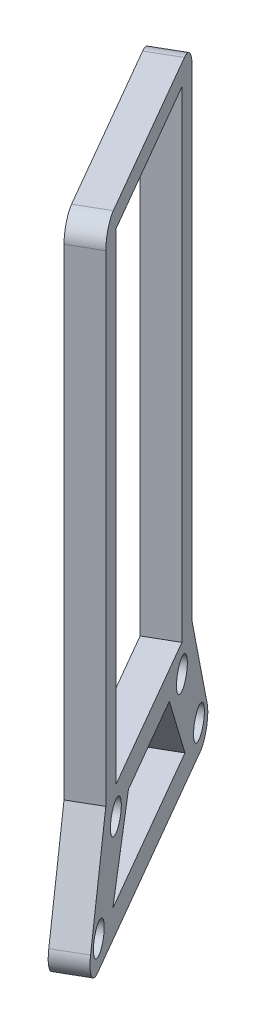
SolidWorks part; units mm, degrees
ref_plane "Front Plane" through (0, 0, 0) normal (0, 0, 1) x (1, 0, 0)
ref_plane "Top Plane" through (0, 0, 0) normal (0, 1, 0) x (1, 0, 0)
ref_plane "Right Plane" through (0, 0, 0) normal (1, 0, 0) x (0, 0, -1)
sketch "Sketch1" plane through (7.0626, 0, -4.0776) normal (-0.866, 0, 0.5) x (0.5, 0, 0.866)
  line L1 (14.4754, 136.7988) -> (48.7221, 136.7988)
  line L2 (48.7221, 136.7988) -> (56.4954, 118.0559)
  line L3 (56.4954, 118.0559) -> (6.7021, 118.0559)
  line L4 (18.4754, 132.7988) -> (44.7221, 132.7988) construction
  line L5 (17.273, 122.0559) -> (23.4754, 132.7988)
  line L6 (14.4754, 136.7988) -> (14.4754, 209.7988)
  line L7 (18.4754, 206.7988) -> (44.7221, 206.7988)
  line L8 (23.4754, 132.7988) -> (39.7221, 132.7988)
  line L9 (48.7221, 209.7988) -> (48.7221, 136.7988)
  line L10 (39.7221, 132.7988) -> (45.9246, 122.0559)
  line L12 (45.9246, 122.0559) -> (17.273, 122.0559)
  line L13 (37.3927, 132.7988) -> (25.8049, 132.7988) construction
  line L14 (18.4754, 136.7988) -> (18.4754, 206.7988)
  line L15 (14.4754, 136.7988) -> (6.7021, 118.0559)
  line L17 (44.7221, 206.7988) -> (44.7221, 136.7988)
  line L19 (14.4754, 209.7988) -> (48.7221, 209.7988)
  circle A0 centre (18.4754, 132.7988) radius 2.15
  circle A2 centre (51.4954, 122.0559) radius 2.15
  circle A5 centre (11.7021, 122.0559) radius 2.15
  circle A6 centre (44.7221, 132.7988) radius 2.15
  point P0 (11.7021, 122.0559)
  point P2 (51.4954, 122.0559)
  point P4 (44.7221, 132.7988)
  point P6 (18.4754, 132.7988)
  point P15 (44.7221, 205.085)
  point P20 (31.5988, 136.7988)
  point P21 (31.5988, 132.7988)
  point P23 (0, 0)
  dimension "D1" = 4.3
  dimension "D2" = 5
  dimension "D3" = 4
  dimension "D4" = 5
  dimension "D5" = 4
  dimension "D6" = 5
  dimension "D7" = 60
  dimension "D8" = 4
  dimension "D9" = 4
  dimension "D10" = 70
  dimension "D11" = 3
extrude "Boss-Extrude1" add sketch "Sketch1" against normal blind 4.45
fillet "Fillet1" radius 3 4 edges at (37.2372, 118.0559, 43.7364) (12.3405, 118.0559, 0.6141) (33.3505, 209.7988, 37.0045) (16.2272, 209.7988, 7.346)
